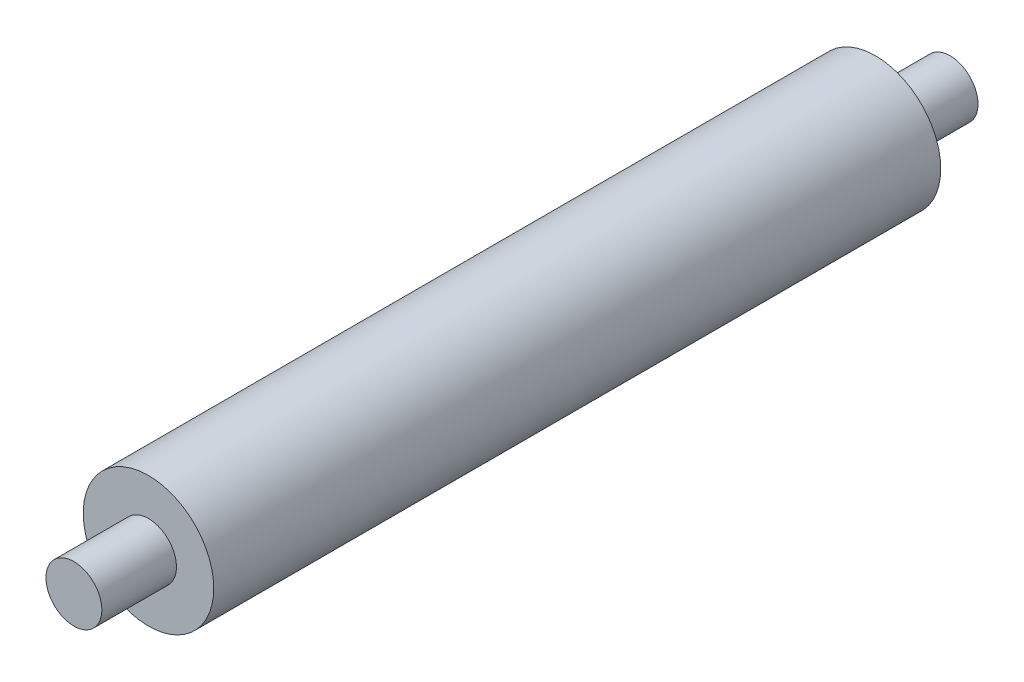
SolidWorks part; units mm, degrees
ref_plane "前视基准面" through (0, 0, 0) normal (0, 0, 1) x (1, 0, 0)
ref_plane "上视基准面" through (0, 0, 0) normal (0, 1, 0) x (1, 0, 0)
ref_plane "右视基准面" through (0, 0, 0) normal (1, 0, 0) x (0, 0, -1)
sketch "草图1" plane through (0, 0, 0) normal (0, 0, 1) x (1, 0, 0)
  circle A0 centre (0, 0) radius 3.5
extrude "凸台-拉伸1" add sketch "草图1" along normal blind 39
sketch "草图2" plane through (0, 0, 39) normal (0, 0, 1) x (1, 0, 0)
  circle A0 centre (0, 0) radius 1.5
  circle A1 centre (0, 0) radius 1.5
extrude "凸台-拉伸3" add sketch "草图2" along normal blind 4 and the other way blind 43 contours A0
